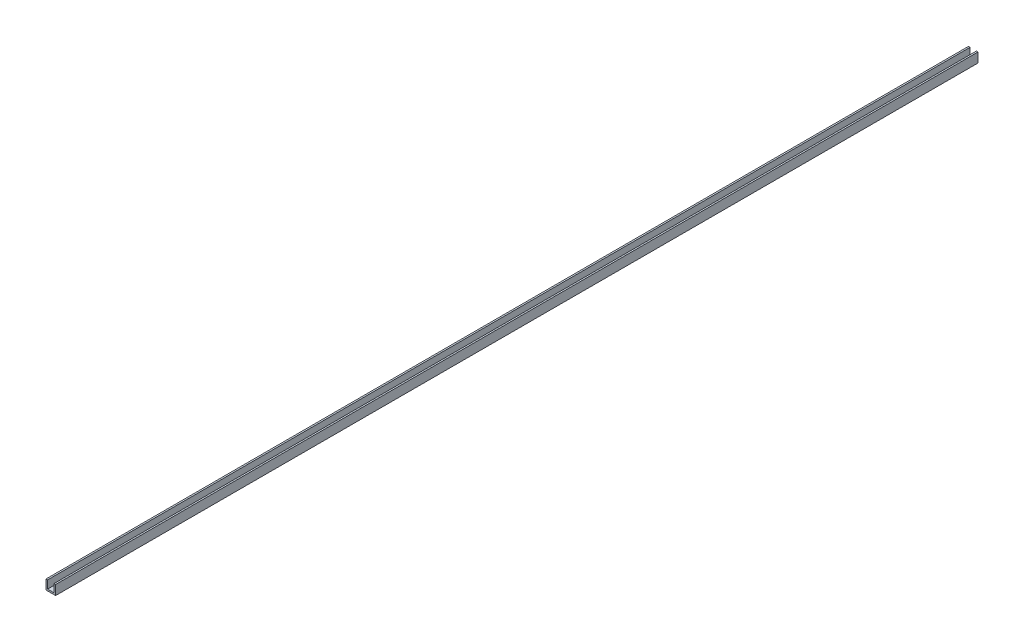
SolidWorks part; units mm, degrees
material "6063-T6"
ref_plane "Front Plane" through (0, 0, 0) normal (0, 0, 1) x (1, 0, 0)
ref_plane "Top Plane" through (0, 0, 0) normal (0, 1, 0) x (1, 0, 0)
ref_plane "Right Plane" through (0, 0, 0) normal (1, 0, 0) x (0, 0, -1)
sketch "Sketch1" plane through (0, 0, 0) normal (0, 0, 1) x (1, 0, 0)
  line L0 (0, 0) -> (0, -19.05)
  line L1 (0, -19.05) -> (19.05, -19.05)
  line L2 (19.05, -19.05) -> (19.05, 0)
  line L3 (19.05, 0) -> (15.875, 0)
  line L4 (15.875, 0) -> (15.875, -15.875)
  line L5 (15.875, -15.875) -> (3.175, -15.875)
  line L6 (3.175, -15.875) -> (3.175, 0)
  line L7 (3.175, 0) -> (0, 0)
  dimension "D1" = 3.175
  dimension "D2" = 19.05
  dimension "D3" = 3.175
extrude "Boss-Extrude1" add sketch "Sketch1" along normal blind 1828.8
